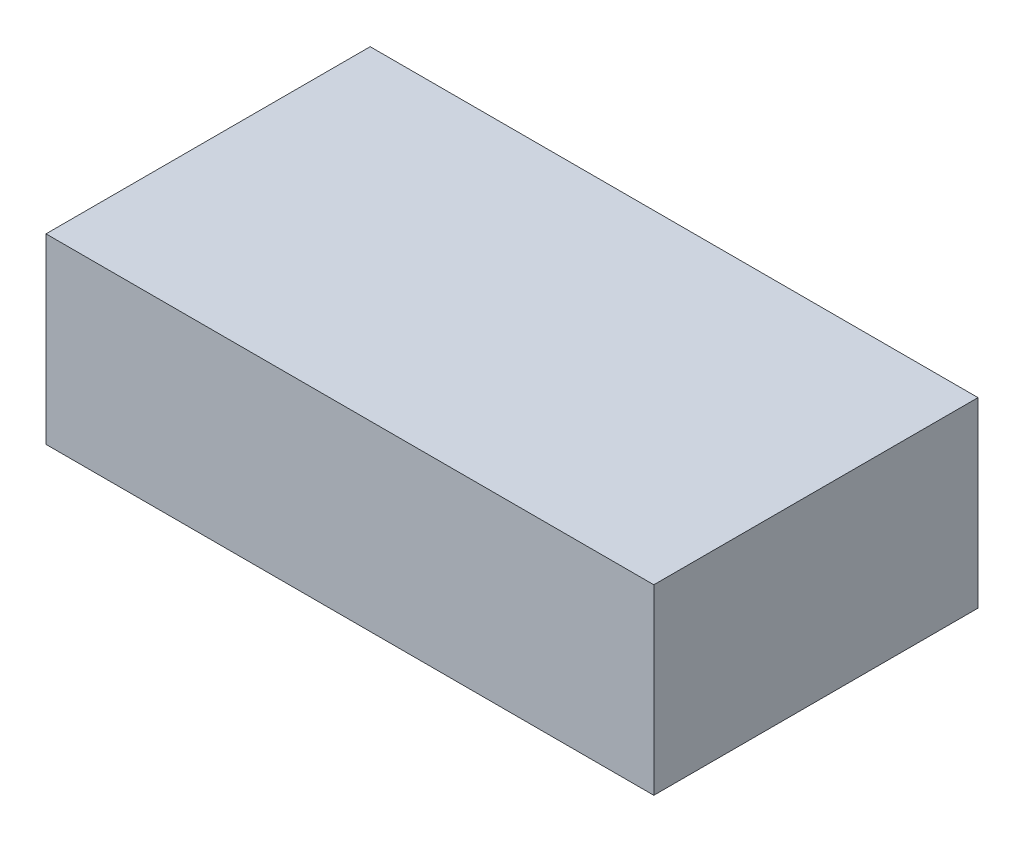
SolidWorks part; units mm, degrees
ref_plane "前视" through (0, 0, 0) normal (0, 0, 1) x (1, 0, 0)
ref_plane "上视" through (0, 0, 0) normal (0, 1, 0) x (1, 0, 0)
ref_plane "右视" through (0, 0, 0) normal (1, 0, 0) x (0, 0, -1)
sketch "草图1" plane through (0, 0, 0) normal (0, 1, 0) x (1, 0, 0)
  line L1 (-75, 40) -> (75, 40)
  line L2 (-75, 40) -> (-75, -40)
  line L3 (-75, -40) -> (75, -40)
  line L4 (75, 40) -> (75, -40)
  line L5 (-75, 40) -> (75, -40) construction
  line L6 (-75, -40) -> (75, 40) construction
  point P0 (0, 0)
  dimension "D1" = 150
  dimension "D2" = 80
extrude "凸台-拉伸1" add sketch "草图1" along normal blind 45
sketch "草图2" plane through (0, 0, 0) normal (0, -1, 0) x (1, 0, 0)
  line L0 (0, 0) -> (38, 0) construction
  line L2 (0, 0) -> (0, 40) construction
  line L3 (-75, 40) -> (75, 40) construction
  circle A0 centre (38, 0) radius 32.5
  circle A1 centre (38, 0) radius 20.5
  circle A2 centre (-38, 0) radius 20.5
  circle A3 centre (-38, 0) radius 32.5
  dimension "D1" = 65
  dimension "D2" = 12
  dimension "D3" = 38
extrude "切除-拉伸1" cut sketch "草图2" against normal blind 1.5
